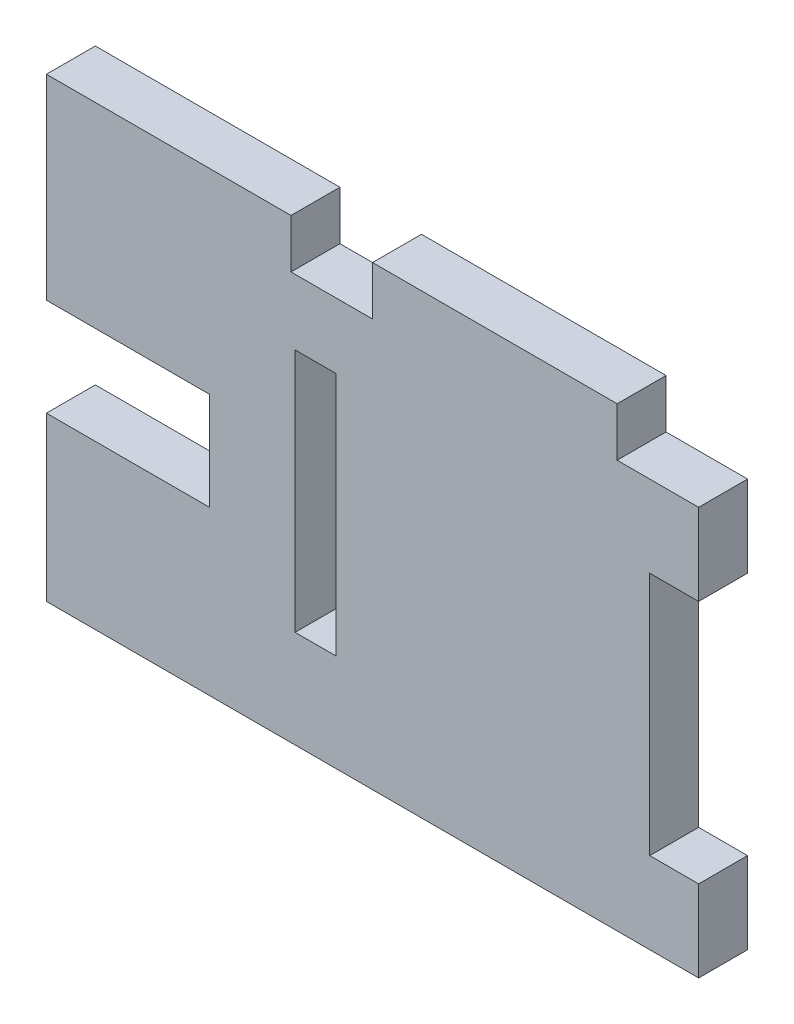
SolidWorks part; units mm, degrees
ref_plane "Front Plane" through (0, 0, 0) normal (0, 0, 1) x (1, 0, 0)
ref_plane "Top Plane" through (0, 0, 0) normal (0, 1, 0) x (1, 0, 0)
ref_plane "Right Plane" through (0, 0, 0) normal (1, 0, 0) x (0, 0, -1)
sketch "Sketch2" plane through (0, 0, 0) normal (0, 0, 1) x (1, 0, 0)
  line L0 (-22.0738, 7.8629) -> (-22.0738, 10.8629)
  line L1 (17.9262, 7.8629) -> (12.9262, 7.8629)
  line L2 (17.9262, 7.8629) -> (17.9262, -17.1371)
  line L3 (17.9262, -17.1371) -> (-32.0738, -17.1371)
  line L4 (-32.0738, 7.8629) -> (-32.0738, -17.1371)
  line L5 (17.9262, 2.8629) -> (14.9262, 2.8629)
  line L6 (-22.0738, 10.8629) -> (-7.0738, 10.8629)
  line L7 (17.9262, -12.1371) -> (14.9262, -12.1371)
  line L8 (14.9262, 2.8629) -> (14.9262, -12.1371)
  line L9 (-4.3238, -11.1532) -> (-6.8238, -11.1532)
  line L10 (-4.3238, -11.1532) -> (-4.3238, 3.8468)
  line L11 (-4.3238, 3.8468) -> (-6.8238, 3.8468)
  line L12 (-6.8238, -11.1532) -> (-6.8238, 3.8468)
  line L13 (-27.0738, -1.1371) -> (-12.0738, -1.1371)
  line L14 (-27.0738, -1.1371) -> (-27.0738, -7.1371)
  line L15 (-27.0738, -7.1371) -> (-12.0738, -7.1371)
  line L16 (-12.0738, -1.1371) -> (-12.0738, -7.1371)
  line L17 (-7.0738, 10.8629) -> (-7.0738, 7.8629)
  line L18 (-2.0738, 7.8629) -> (-2.0738, 10.8629)
  line L19 (-2.0738, 10.8629) -> (12.9262, 10.8629)
  line L20 (12.9262, 10.8629) -> (12.9262, 7.8629)
  line L21 (-22.0738, 7.8629) -> (-32.0738, 7.8629)
  line L22 (-2.0738, 7.8629) -> (-7.0738, 7.8629)
  point P8 (-4.3238, -3.8952)
  dimension "D1" = 3
  dimension "D2" = 15
  dimension "D3" = 22.25
  dimension "D4" = 2.5
  dimension "D5" = 15
  dimension "D6" = 6
  dimension "D7" = 15
  dimension "D8" = 3
  dimension "D9" = 15
  dimension "D10" = 3
  dimension "D11" = 15
  dimension "D12" = 5
  dimension "D13" = 5
  dimension "D14" = 5
  dimension "D15" = 10
  dimension "D16" = 5
  dimension "D17" = 5
  dimension "D18" = 10
  dimension "D19" = 50
extrude "Boss-Extrude1" add sketch "Sketch2" along normal blind 3 contours L18 L22 L17 L6 L0 L21 L4 L3 L2 L7 L8 L5 L1 L20 L19 L13 L16 L15 L14 L9 L12 L11 L10
sketch "Sketch4" plane through (0, 0, 3) normal (0, 0, 1) x (1, 0, 0)
  line L0 (-22.0738, 1.8629) -> (-22.0738, 7.8629)
  line L1 (17.9262, -17.1371) -> (-32.0738, -17.1371) construction
  line L2 (-22.0738, 7.8629) -> (-32.0738, 7.8629)
  line L3 (-22.0738, -17.1371) -> (-22.0738, 1.8629)
  line L4 (-32.0738, 7.8629) -> (-32.0738, 1.8629)
  line L5 (-22.0738, -17.1371) -> (-32.0738, -17.1371)
  line L6 (-32.0738, -17.1371) -> (-32.0738, 1.8629)
  line L7 (-32.0738, 7.8629) -> (-32.0738, -17.1371) construction
extrude "Cut-Extrude1" cut sketch "Sketch4" against normal through all
